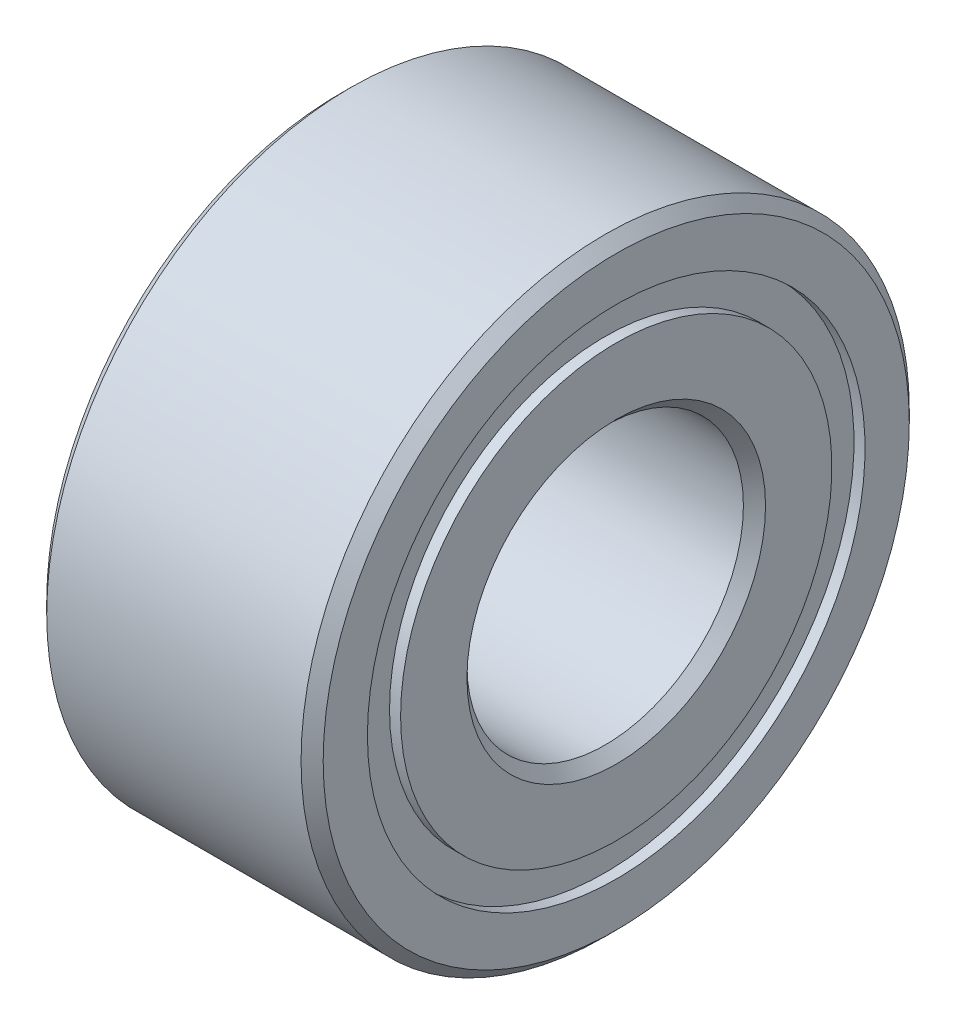
SolidWorks part; units mm, degrees
ref_plane "Front Plane" through (0, 0, 0) normal (0, 0, 1) x (1, 0, 0)
ref_plane "Top Plane" through (0, 0, 0) normal (0, 1, 0) x (1, 0, 0)
ref_plane "Right Plane" through (0, 0, 0) normal (1, 0, 0) x (0, 0, -1)
sketch "Sketch1" plane through (0, 0, 0) normal (0, 0, 1) x (1, 0, 0)
  line L0 (0, 4) -> (0, 0) construction
  line L1 (2.5, 5.5) -> (-2.5, 5.5)
  line L2 (2.5, 5.5) -> (2.5, 2.5) construction
  line L3 (2.5, 2.5) -> (-2.5, 2.5)
  line L4 (-2.5, 5.5) -> (-2.5, 4.5)
  line L5 (2.5, 5.5) -> (-2.5, 2.5) construction
  line L6 (2.5, 2.5) -> (-2.5, 5.5) construction
  line L7 (-9.5787, 0) -> (1.12, 0) construction
  line L8 (-2.5, 3.9) -> (-2.5, 2.5)
  line L9 (-2.5, 4.5) -> (-2.3, 4.5)
  line L11 (-2.5, 3.9) -> (-2.3, 3.9)
  line L12 (-2.3, 4.5) -> (-2.3, 3.9)
  line L13 (2.5, 3.9) -> (2.5, 2.5)
  line L14 (2.5, 3.9) -> (2.3, 3.9)
  line L15 (2.3, 4.5) -> (2.3, 3.9)
  line L16 (2.5, 4.5) -> (2.3, 4.5)
  line L17 (2.5, 5.5) -> (2.5, 4.5)
  point P0 (0, 4)
  dimension "D1" = 5
  dimension "D3" = 2.5
  dimension "D2" = 5.5
  dimension "D4" = 1
  dimension "D5" = 1.4
  dimension "D6" = 0.2
revolve "Revolve1" add sketch "Sketch1" angle 360 about L7
chamfer "Chamfer1" distance 0.2 angle 45 4 edges at (2.5, 0, 5.5) (-2.5, 0, 5.5) (-2.5, 0, 2.5) (2.5, 0, 2.5)
sketch "Sketch2" [suppressed] plane through (0, 0, 0) normal (0, 0, 1) x (1, 0, 0)
  line L0 (-3.9525, 0) -> (5.8197, 0) construction
  line L1 (2, 4.8) -> (1, 4.8)
  line L2 (2, 4.8) -> (2, 5.8)
  line L3 (2, 5.8) -> (1, 5.8)
  line L4 (1, 4.8) -> (1, 5.8)
  dimension "D1" = 1
  dimension "D2" = 5.8
revolve "Revolve2" [suppressed] add sketch "Sketch2" angle 360 about L0
chamfer "Chamfer2" [suppressed] distance 0.2 angle 45
sketch "Sketch3" plane through (0, 0, 0) normal (1, 0, 0) x (0, 0, -1)
  point P0 (0, 0)
equation "\"Width\"= 5mm"
equation "\"InnerDiameter\"= 5mm"
equation "\"OuterDiameter\"= 11mm"
equation "\"D2@Sketch1\"=\"OuterDiameter\"/2"
equation "\"D3@Sketch1\"=\"InnerDiameter\"/2"
equation "\"D1@Sketch1\"=\"Width\""
